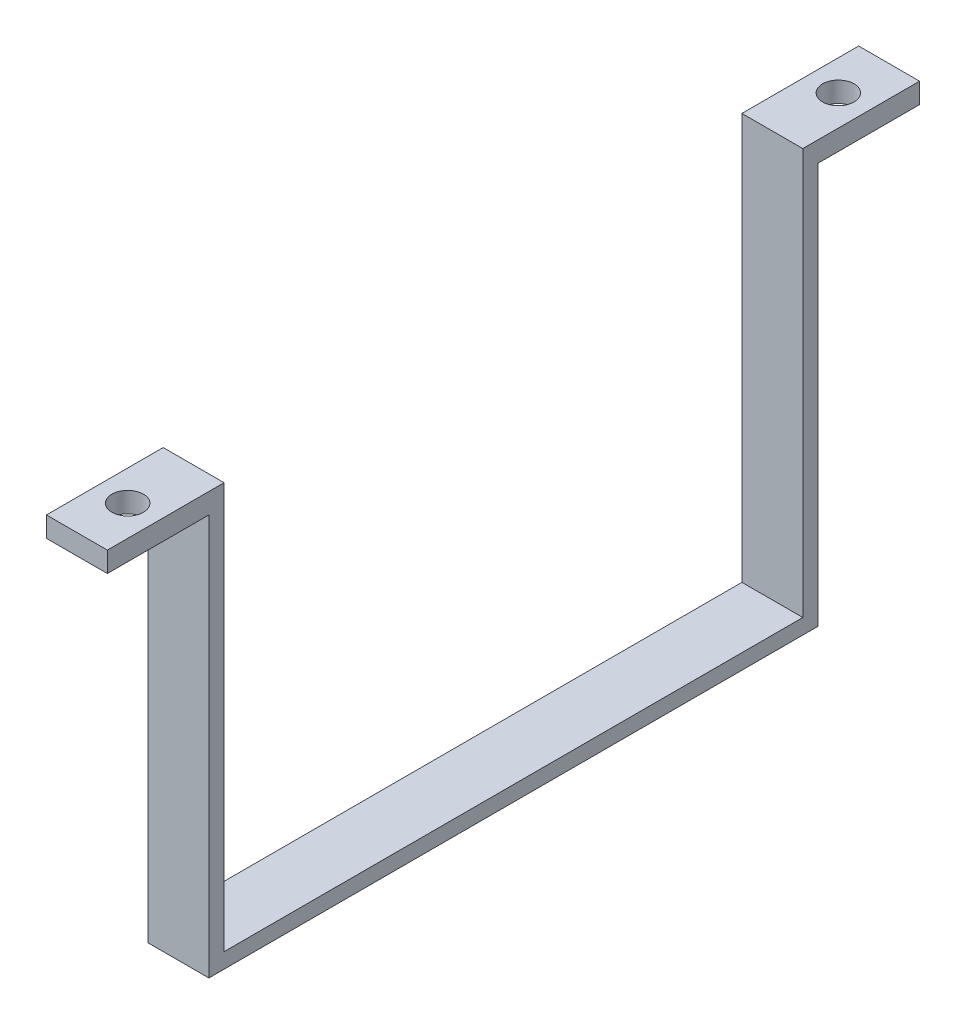
SolidWorks part; units mm, degrees
ref_plane "Płaszczyzna przednia" through (0, 0, 0) normal (0, 0, 1) x (1, 0, 0)
ref_plane "Płaszczyzna górna" through (0, 0, 0) normal (0, 1, 0) x (1, 0, 0)
ref_plane "Płaszczyzna prawa" through (0, 0, 0) normal (1, 0, 0) x (0, 0, -1)
sketch "Sketch1" plane through (0, 0, 0) normal (0, 1, 0) x (1, 0, 0)
  line L9 (-25, -40) -> (25, -40)
  line L16 (-25, -40) -> (-25, 40)
  line L21 (-25, 40) -> (25, 40)
  line L23 (25, -40) -> (25, 40)
  line L24 (-23.5, -28.5) -> (23.5, -28.5)
  line L25 (-23.5, -28.5) -> (-23.5, 28.5)
  line L26 (-25, -30) -> (25, -30)
  line L27 (-25, -30) -> (-25, 30)
  line L28 (-25, 30) -> (25, 30)
  line L29 (25, -30) -> (25, 30)
  line L30 (-23.5, 28.5) -> (23.5, 28.5)
  line L31 (23.5, -28.5) -> (23.5, 28.5)
  line L32 (-23.5, -28.5) -> (23.5, 28.5) construction
  line L33 (-23.5, 28.5) -> (23.5, -28.5) construction
  point P0 (0, 0)
  point P1 (0, 0)
  point P5 (0, 0)
  point P8 (0, 0)
  point P11 (0, 0)
  point P14 (0, 0)
  dimension "D1" = 50
  dimension "D2" = 80
  dimension "D3" = 50
  dimension "D4" = 60
  dimension "D5" = 47
  dimension "D6" = 57
extrude "Boss-Extrude6" add sketch "Sketch1" along normal blind 40 contours L28 L16 L26 L23 L31 L24 L25 L30
sketch "Sketch7" plane through (0, 0, 0) normal (0, -1, 0) x (1, 0, 0)
  line L1 (-25, 30) -> (25, 30)
  line L2 (-25, 30) -> (-25, -30)
  line L3 (-25, -30) -> (25, -30)
  line L4 (25, 30) -> (25, -30)
extrude "Boss-Extrude8" add sketch "Sketch7" along normal blind 1.5
sketch "Sketch8" plane through (25, 0, 0) normal (1, 0, 0) x (0, 0, -1)
  line L1 (-30, 40) -> (-40, 40)
  line L2 (-30, 40) -> (-30, 38)
  line L3 (-30, 38) -> (-40, 38)
  line L4 (-40, 40) -> (-40, 38)
  line L5 (30, 40) -> (40, 40)
  line L6 (30, 40) -> (30, 38)
  line L7 (30, 38) -> (40, 38)
  line L8 (40, 40) -> (40, 38)
  dimension "D1" = 10
  dimension "D2" = 2
  dimension "D3" = 10
  dimension "D4" = 2
extrude "Boss-Extrude9" add sketch "Sketch8" against normal blind 50
sketch "Sketch9" plane through (0, 40, 0) normal (0, 1, 0) x (1, 0, 0)
  circle A0 centre (-20, 35) radius 1.55
  circle A1 centre (20, 35) radius 1.55
  circle A2 centre (20, -35) radius 1.55
  circle A3 centre (-20, -35) radius 1.55
  point P0 (0, 0)
  dimension "D1" = 40
  dimension "D2" = 70
extrude "Cut-Extrude1" cut sketch "Sketch9" against normal blind 3
sketch "Sketch11" plane through (-25, 0, 0) normal (-1, 0, 0) x (0, 0, 1)
  line L0 (-30, 18.25) -> (30, 18.25) construction
  line L1 (-30, 38) -> (-30, -1.5) construction
  line L2 (30, 38) -> (30, -1.5) construction
  line L4 (40, 40) -> (-40, 40) construction
  line L5 (0, 40) -> (0, -1.5) construction
  line L6 (30, -1.5) -> (-30, -1.5) construction
  circle A0 centre (0, 18.25) radius 8.25
  point P6 (0, 18.25)
extrude "Cut-Extrude3" cut sketch "Sketch11" against normal blind 1.5
sketch "Sketch12" plane through (-25, 0, 0) normal (-1, 0, 0) x (0, 0, 1)
  line L0 (-40, 40) -> (40, 40)
  line L1 (-40, 40) -> (-40, -2.4288)
  line L2 (40, 40) -> (40, -2.4288)
  line L3 (-40, -2.4288) -> (40, -2.4288)
extrude "Cut-Extrude4" cut sketch "Sketch12" against normal blind 2
sketch "Sketch13" plane through (25, 0, 0) normal (1, 0, 0) x (0, 0, -1)
  line L1 (-46.3371, 45.7156) -> (46.4358, 45.7156)
  line L2 (-46.3371, 45.7156) -> (-46.3371, -11.6834)
  line L3 (-46.3371, -11.6834) -> (46.4358, -11.6834)
  line L4 (46.4358, 45.7156) -> (46.4358, -11.6834)
extrude "Cut-Extrude5" cut sketch "Sketch13" against normal blind 42
